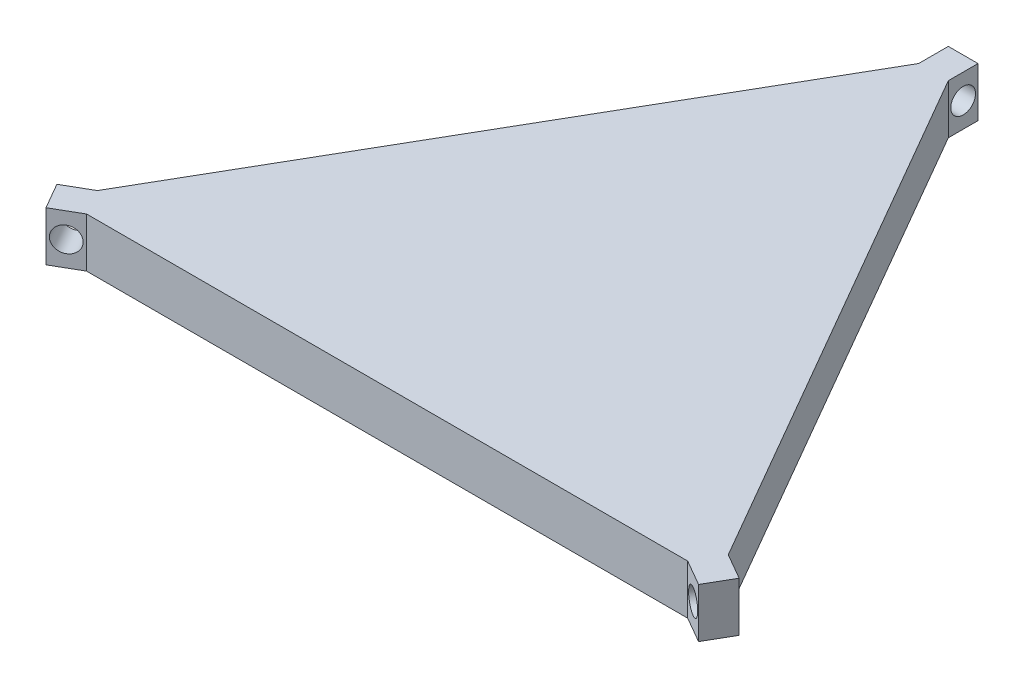
SolidWorks part; units mm, degrees
ref_plane "Front Plane" through (0, 0, 0) normal (0, 0, 1) x (1, 0, 0)
ref_plane "Top Plane" through (0, 0, 0) normal (0, 1, 0) x (1, 0, 0)
ref_plane "Right Plane" through (0, 0, 0) normal (1, 0, 0) x (0, 0, -1)
sketch "Sketch1" plane through (0, 0, 0) normal (0, 1, 0) x (1, 0, 0)
  line L6 (-3, 110.3836) -> (-63.73, 5.1962)
  line L7 (3, 110.3836) -> (63.73, 5.1962)
  line L8 (-60.73, 0) -> (60.73, 0)
  line L10 (-63.73, 5.1962) -> (-68.9262, 2.1962)
  line L11 (-60.73, 0) -> (-65.9262, -3)
  line L12 (-68.9262, 2.1962) -> (-65.9262, -3)
  line L14 (60.73, 0) -> (65.9262, -3)
  line L15 (63.73, 5.1962) -> (68.9262, 2.1962)
  line L16 (65.9262, -3) -> (68.9262, 2.1962)
  line L18 (3, 110.3836) -> (3, 116.3836)
  line L19 (-3, 110.3836) -> (-3, 116.3836)
  line L20 (3, 116.3836) -> (-3, 116.3836)
  point P1 (0, 0)
  dimension "D1" = 6
  dimension "D2" = 210
  dimension "D3" = 210
  dimension "D4" = 210
  dimension "D5" = 210
  dimension "D6" = 210
  dimension "D7" = 210
  dimension "D8" = 90
  dimension "D9" = 6
  dimension "D10" = 121.46
extrude "Boss-Extrude1" add sketch "Sketch1" along normal blind 10
sketch "Sketch2" plane through (-15.1825, 0, -26.2969) normal (0.5, 0, 0.866) x (0.866, 0, -0.5)
  line L0 (-58.5937, 10) -> (-52.5937, 10) construction
  line L1 (-58.5937, 10) -> (-58.5937, 0) construction
  circle A0 centre (-55.5937, 5) radius 2.5
  point P4 (-55.5937, 10)
  point P7 (-58.5937, 5)
  dimension "5" = 5
extrude "Cut-Extrude1" cut sketch "Sketch2" against normal up to surface (134.326 mm away)
ref_plane "Plane2" through (16.6825, 0, -28.8949) normal (-0.5, 0, 0.866) x (0.866, 0, 0.5)
ref_plane "Plane3" through (0, 0, 0) normal (-1, 0, 0) x (0, 0, 1)
mirror "Mirror6" about plane through (0, 0, 0) normal (-1, 0, 0) of "Cut-Extrude1"
ref_plane "Plane4" through (-16.6825, 0, -28.8949) normal (0.5, 0, 0.866) x (0.866, 0, -0.5)
sketch "Sketch3" plane through (-3, 0, 0) normal (-1, 0, 0) x (0, 0, 1)
  line L0 (-116.3836, 10) -> (-116.3836, 0) construction
  line L1 (-116.3836, 0) -> (-110.3836, 0) construction
  circle A0 centre (-113.3836, 5) radius 2.5
  dimension "D3" = 5
  dimension "D1" = 3
  dimension "D2" = 5
extrude "Cut-Extrude2" cut sketch "Sketch3" against normal up to surface (6 mm away) up to face at (3, 5, -113.3836)
